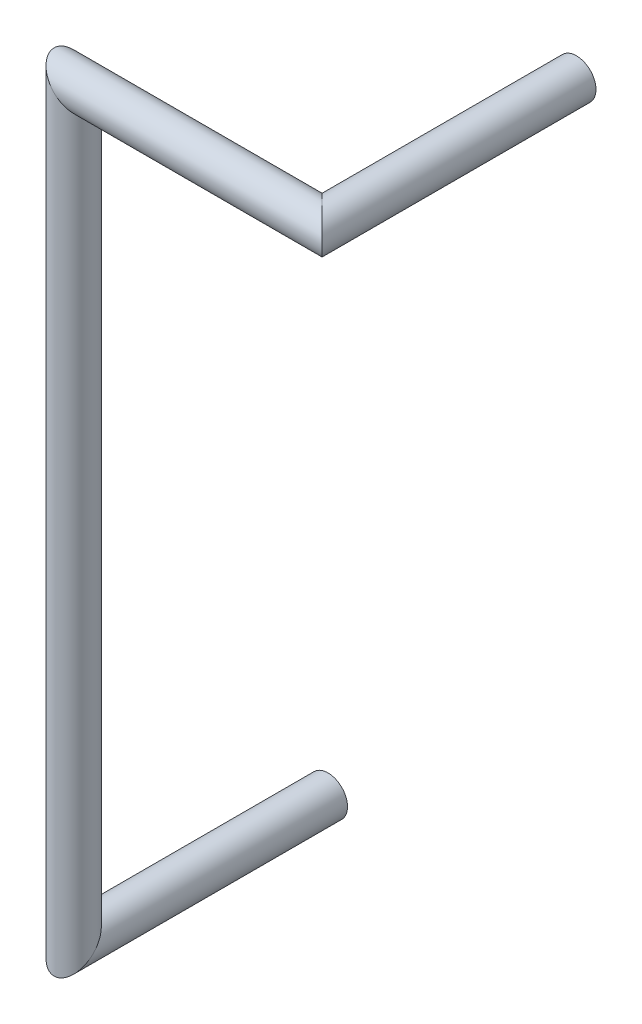
SolidWorks part; units mm, degrees
ref_plane "Front Plane" through (0, 0, 0) normal (0, 0, 1) x (1, 0, 0)
ref_plane "Top Plane" through (0, 0, 0) normal (0, 1, 0) x (1, 0, 0)
ref_plane "Right Plane" through (0, 0, 0) normal (1, 0, 0) x (0, 0, -1)
sketch3d "3DSketch3"
  line L0 (0, 0, 0) -> (0, 0, 2.6)
  line L1 (0, 0, 2.6) -> (0, 7.62, 2.6)
  line L2 (0, 7.62, 2.6) -> (2.54, 7.62, 2.6)
  line L3 (2.54, 7.62, 2.6) -> (2.54, 7.62, 0)
  dimension "D2" = 2.6
  dimension "D1" = 2.6
  dimension "D3" = 7.62
  dimension "D4" = 2.54
sweep "Sweep1" add path "3DSketch3" circular profile diameter 0.4 parameters "D3"=0.4
equation "\"D2@3DSketch3\"=\"D1@3DSketch3\""
